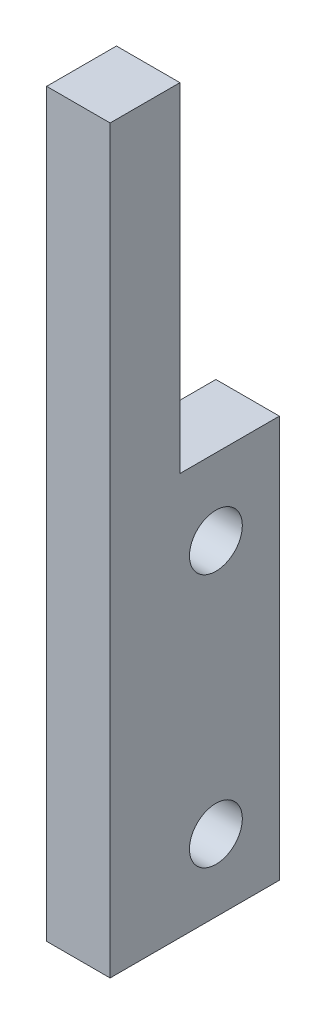
SolidWorks part; units mm, degrees
ref_plane "Front Plane" through (0, 0, 0) normal (0, 0, 1) x (1, 0, 0)
ref_plane "Top Plane" through (0, 0, 0) normal (0, 1, 0) x (1, 0, 0)
ref_plane "Right Plane" through (0, 0, 0) normal (1, 0, 0) x (0, 0, -1)
sketch "Sketch1" plane through (0, 0, 0) normal (1, 0, 0) x (0, 0, -1)
  line L0 (0, 0) -> (0, 35)
  line L1 (0, 35) -> (3.3, 35)
  line L2 (3.3, 35) -> (3.3, 19)
  line L3 (3.3, 19) -> (8, 19)
  line L4 (8, 19) -> (8, 0)
  line L5 (8, 0) -> (0, 0)
  dimension "D1" = 35
  dimension "D2" = 19
  dimension "D3" = 8
  dimension "D5" = 4.7
extrude "Boss-Extrude1" add sketch "Sketch1" along normal blind 3
hole_wizard "Tap Drill for M3x0.5 Tap1" positions "Sketch3" profile "Sketch2" hole size "M3x0.5" standard "ANSI Metric" end condition up to next
sketch "Sketch3" plane through (3, 0, 0) normal (1, 0, 0) x (0, 0, -1)
  line L0 (0, 35) -> (0, 0) construction
  line L1 (0, 0) -> (8, 0) construction
  point P0 (5, 15.4)
  point P2 (5, 3.4)
  dimension "D1" = 5
  dimension "D2" = 3.4
  dimension "D3" = 15.4
sketch "Sketch2" plane through (3, 15.4, -5) normal (0, 1, 0) x (0, 0, -1)
  line L0 (0, 0) -> (0, 3)
  line L1 (0, 3) -> (1.25, 3)
  line L2 (1.25, 3) -> (1.25, 0)
  line L5 (1.25, 0) -> (0, 0)
  line L11 (0, -6.35) -> (0, 107.95) construction
  dimension "Thru Hole Dia." = 2.5
  dimension "Thru Hole Depth" = 3
